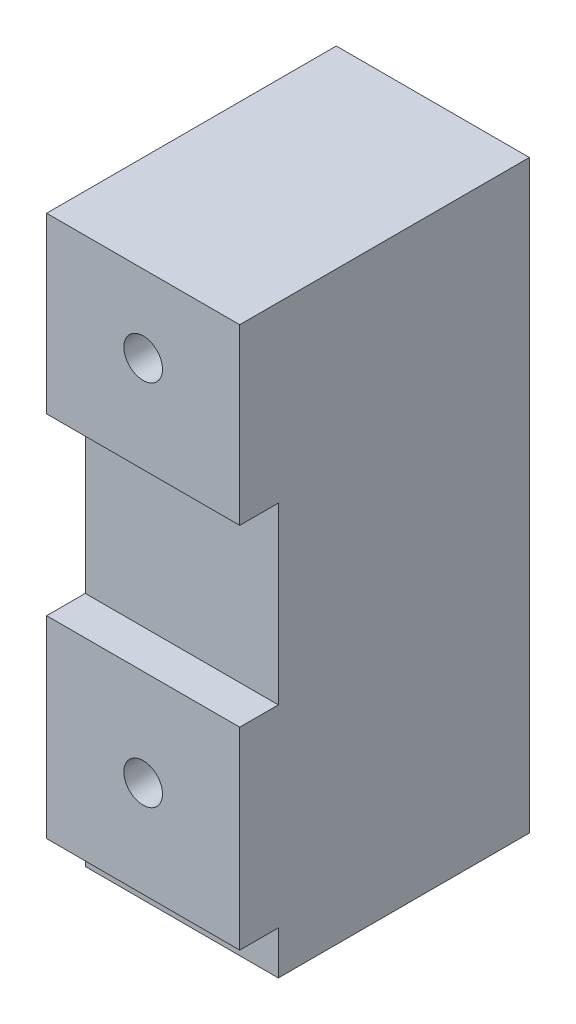
SolidWorks part; units mm, degrees
ref_plane "Front Plane" through (0, 0, 0) normal (0, 0, 1) x (1, 0, 0)
ref_plane "Top Plane" through (0, 0, 0) normal (0, 1, 0) x (1, 0, 0)
ref_plane "Right Plane" through (0, 0, 0) normal (1, 0, 0) x (0, 0, -1)
sketch "Sketch1" plane through (0, 0, 0) normal (0, 0, 1) x (1, 0, 0)
  line L0 (0, 19.05) -> (0, 0) construction
  line L2 (-5, 23.05) -> (5, 23.05)
  line L3 (-5, 23.05) -> (-5, -4)
  line L4 (-5, -4) -> (5, -4)
  line L5 (5, 23.05) -> (5, -4)
  line L6 (0, -4) -> (0, 23.05) construction
  line L7 (-5, 9.525) -> (5, 9.525) construction
  line L8 (-5, -4) -> (5, -4)
  line L9 (-5, -4) -> (-5, -7.25)
  line L10 (-5, -7.25) -> (5, -7.25)
  line L11 (5, -4) -> (5, -7.25)
  line L12 (0, -7.25) -> (0, -4) construction
  line L13 (-5, -5.625) -> (5, -5.625) construction
  circle A0 centre (0, 0) radius 1
  circle A1 centre (0, 19.05) radius 1
  point P12 (0, 0)
  point P78 (0, -5.625)
  point P173 (0, 9.525)
  dimension "D1" = 7.25
  dimension "D2" = 2
  dimension "D3" = 19.05
  dimension "D4" = 4
  dimension "D5" = 10
extrude "Boss-Extrude1" add sketch "Sketch1" against normal blind 15 contours L5 L2 L3 L4 A1 A0 | L11 L4 L9 L10
sketch "Sketch2" plane through (0, 0, 0) normal (0, 0, 1) x (1, 0, 0)
  line L0 (5, 23.05) -> (5, -7.25) construction
  line L1 (-5, 24.05) -> (5, 24.05)
  line L2 (-5, 24.05) -> (-5, 14.05)
  line L3 (-5, 14.05) -> (5, 14.05)
  line L4 (5, 24.05) -> (5, 14.05)
  line L5 (0, 14.05) -> (0, 24.05) construction
  line L6 (-5, 19.05) -> (5, 19.05) construction
  line L8 (-5, -5) -> (5, -5)
  line L9 (-5, -5) -> (-5, 5)
  line L10 (-5, 5) -> (5, 5)
  line L11 (5, -5) -> (5, 5)
  line L12 (0, 5) -> (0, -5) construction
  line L13 (-5, 0) -> (5, 0) construction
  point P0 (0, 19.05)
  point P6 (0, 0)
extrude "Cut-Extrude1" cut sketch "Sketch2" against normal blind 2 flip side to cut
